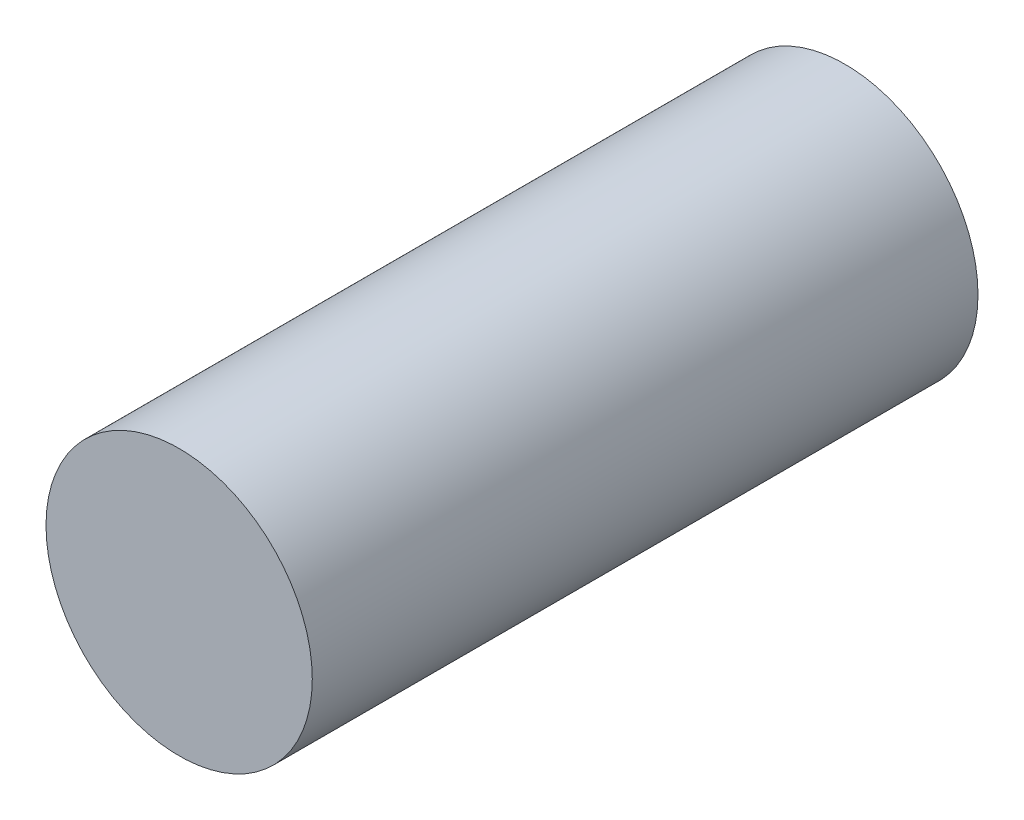
SolidWorks part; units mm, degrees
ref_plane "Front Plane" through (0, 0, 0) normal (0, 0, 1) x (1, 0, 0)
ref_plane "Top Plane" through (0, 0, 0) normal (0, 1, 0) x (1, 0, 0)
ref_plane "Right Plane" through (0, 0, 0) normal (1, 0, 0) x (0, 0, -1)
sketch "Sketch1" plane through (0, 0, 0) normal (0, 0, 1) x (1, 0, 0)
  circle A0 centre (0, 0) radius 1
extrude "Boss-Extrude2" add sketch "Sketch1" along normal blind 5 contours A0
